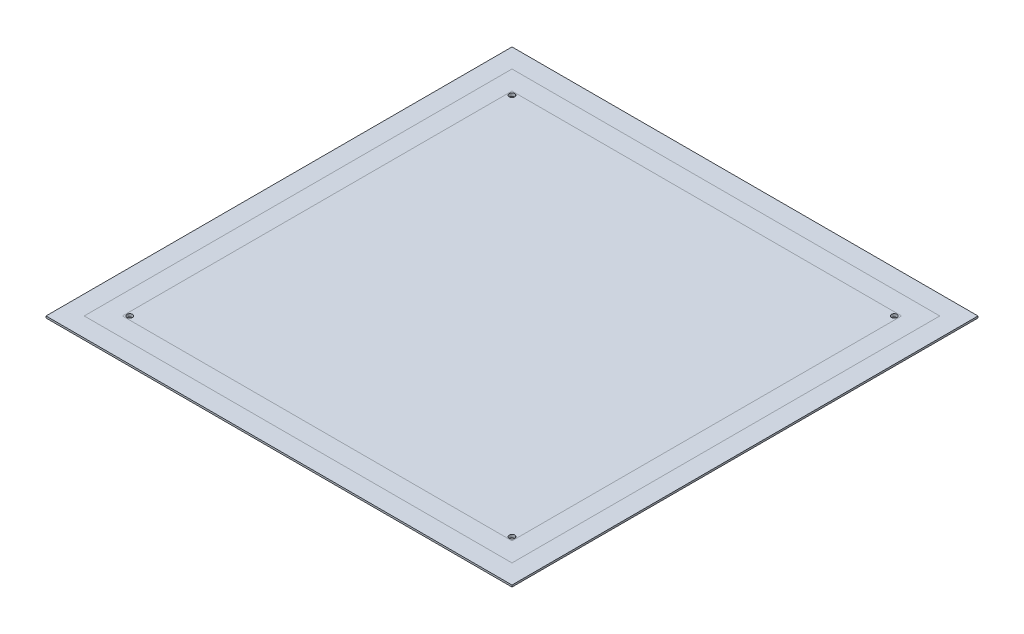
SolidWorks part; units mm, degrees
ref_plane "Front Plane" through (0, 0, 0) normal (0, 0, 1) x (1, 0, 0)
ref_plane "Top Plane" through (0, 0, 0) normal (0, 1, 0) x (1, 0, 0)
ref_plane "Right Plane" through (0, 0, 0) normal (1, 0, 0) x (0, 0, -1)
sketch "Sketch1" plane through (0, 0, 0) normal (0, 1, 0) x (1, 0, 0)
  line L1 (107, 107) -> (-107, 107)
  line L2 (107, 107) -> (107, -107)
  line L3 (107, -107) -> (-107, -107)
  line L4 (-107, 107) -> (-107, -107)
  line L5 (0, -107) -> (0, 107) construction
  line L6 (107, 0) -> (-107, 0) construction
  point P0 (0, 0)
  dimension "D1" = 214
  dimension "D2" = 214
extrude "Boss-Extrude1" add sketch "Sketch1" along normal blind 1.6 contours L2 L3 L4 L1
hole_wizard "M2.5 Clearance Hole1" positions "Sketch4" profile "Sketch3" hole size "M2.5" standard "ANSI Metric"
sketch "Sketch4" plane through (0, 1.6, 0) normal (0, 1, 0) x (1, 0, 0)
  line L0 (-105, 105) -> (105, 105) construction
  line L1 (-105, 105) -> (-105, -105) construction
  line L2 (-107, 107) -> (-107, -107) construction
  line L3 (107, 107) -> (-107, 107) construction
  point P0 (-105, 105)
  point P7 (105, 105)
  point P8 (105, -105)
  point P9 (-105, -105)
  dimension "D3" = 90
  dimension "D4" = 210
  dimension "D5" = 210
  dimension "D6" = 2
  dimension "D7" = 2
  dimension "D1" = 2
  dimension "D2" = 2
sketch "Sketch3" plane through (-105, 1.6, -105) normal (1, 0, 0) x (0, 0, 1)
  line L0 (0, 0) -> (0, 12.8693)
  line L1 (0, 12.8693) -> (1.55, 11.938)
  line L2 (1.55, 11.938) -> (1.55, 0)
  line L5 (1.55, 0) -> (0, 0)
  line L10 (0, 12.8693) -> (-1.55, 11.938) construction
  line L11 (0, -6.35) -> (0, 107.95) construction
  dimension "Hole Dia." = 3.1
  dimension "Hole Depth" = 11.938
  dimension "Drill Angle" = 118
sketch "Sketch5" plane through (0, 1.6, 0) normal (0, 1, 0) x (1, 0, 0)
  line L1 (117.5, 117.5) -> (-117.5, 117.5)
  line L2 (117.5, 117.5) -> (117.5, -117.5)
  line L3 (117.5, -117.5) -> (-117.5, -117.5)
  line L4 (-117.5, 117.5) -> (-117.5, -117.5)
  line L5 (0, -117.5) -> (0, 117.5) construction
  line L6 (117.5, 0) -> (-117.5, 0) construction
  line L10 (107, 107) -> (-107, 107)
  line L11 (-107, 107) -> (-107, -107)
  line L12 (-107, -107) -> (107, -107)
  line L13 (107, -107) -> (107, 107)
  line L14 (107, 107) -> (-107, 107)
  line L15 (-107, 107) -> (-107, -107)
  line L16 (-107, -107) -> (107, -107)
  line L17 (107, -107) -> (107, 107)
  point P0 (0, 0)
  dimension "D1" = 235
  dimension "D2" = 235
  dimension "D3" = 0
extrude "Boss-Extrude2" add sketch "Sketch5" against normal blind 1 separate body
sketch "Sketch6" plane through (0, 1.6, 0) normal (0, 1, 0) x (1, 0, 0)
  line L1 (128, 128) -> (-128, 128)
  line L2 (128, 128) -> (128, -128)
  line L3 (128, -128) -> (-128, -128)
  line L4 (-128, 128) -> (-128, -128)
  line L5 (0, -128) -> (0, 128) construction
  line L6 (128, 0) -> (-128, 0) construction
  line L10 (-117.5, 117.5) -> (-117.5, -117.5)
  line L11 (-117.5, -117.5) -> (117.5, -117.5)
  line L12 (117.5, -117.5) -> (117.5, 117.5)
  line L13 (117.5, 117.5) -> (-117.5, 117.5)
  line L14 (-117.5, 117.5) -> (-117.5, -117.5)
  line L15 (-117.5, -117.5) -> (117.5, -117.5)
  line L16 (117.5, -117.5) -> (117.5, 117.5)
  line L17 (117.5, 117.5) -> (-117.5, 117.5)
  point P0 (0, 0)
  dimension "D1" = 256
  dimension "D2" = 256
  dimension "D3" = 0
extrude "Boss-Extrude3" add sketch "Sketch6" against normal blind 1 separate body
sketch "Sketch7" plane through (0, 1.6, 0) normal (0, 1, 0) x (1, 0, 0)
  line L1 (-155, -155) -> (155, -155)
  line L2 (-155, -155) -> (-155, 155)
  line L3 (-155, 155) -> (155, 155)
  line L4 (155, -155) -> (155, 155)
  line L5 (0, 155) -> (0, -155) construction
  line L6 (-155, 0) -> (155, 0) construction
  line L10 (-128, 128) -> (-128, -128)
  line L11 (-128, -128) -> (128, -128)
  line L12 (128, -128) -> (128, 128)
  line L13 (128, 128) -> (-128, 128)
  line L14 (-128, 128) -> (-128, -128)
  line L15 (-128, -128) -> (128, -128)
  line L16 (128, -128) -> (128, 128)
  line L17 (128, 128) -> (-128, 128)
  point P0 (0, 0)
  dimension "D1" = 310
  dimension "D2" = 310
  dimension "D3" = 0
extrude "Boss-Extrude4" [suppressed] add sketch "Sketch7" against normal blind 1 separate body
sketch "Sketch8" plane through (0, 1.6, 0) normal (0, 1, 0) x (1, 0, 0)
  line L1 (110, 110) -> (-110, 110)
  line L2 (110, 110) -> (110, -110)
  line L3 (110, -110) -> (-110, -110)
  line L4 (-110, 110) -> (-110, -110)
  line L5 (0, -110) -> (0, 110) construction
  line L6 (110, 0) -> (-110, 0) construction
  point P0 (0, 0)
  dimension "D1" = 220
